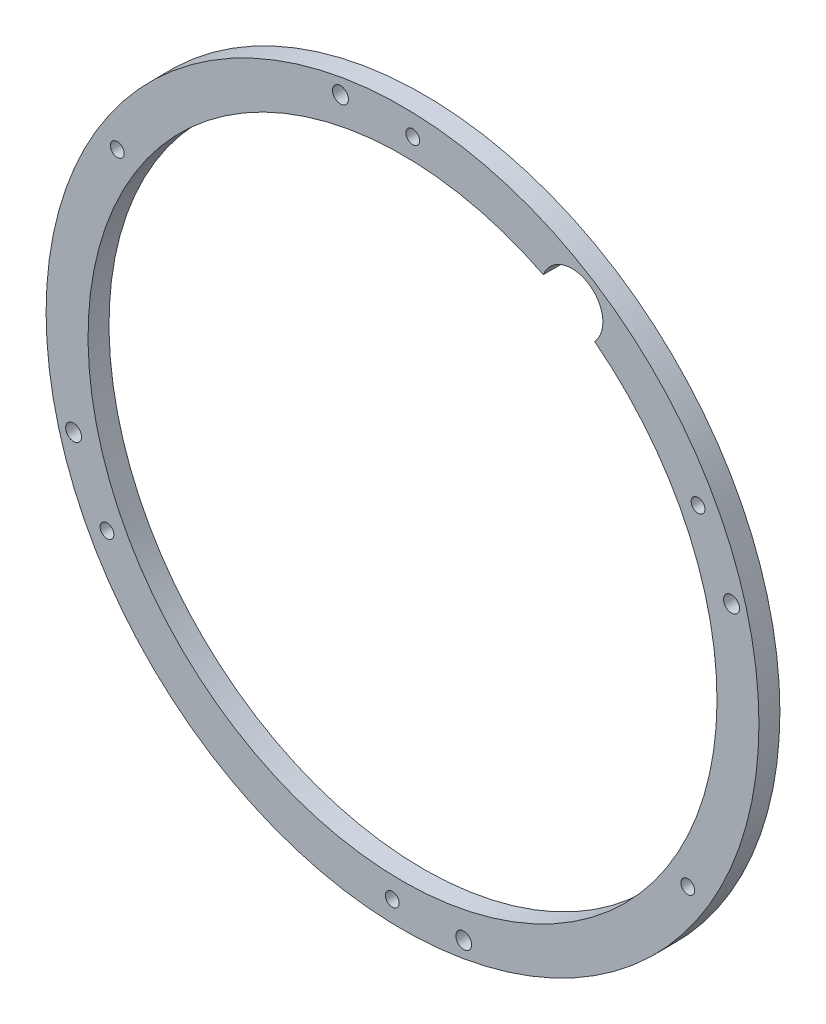
SolidWorks part; units mm, degrees
ref_plane "Front Plane" through (0, 0, 0) normal (0, 0, 1) x (1, 0, 0)
ref_plane "Top Plane" through (0, 0, 0) normal (0, 1, 0) x (1, 0, 0)
ref_plane "Right Plane" through (0, 0, 0) normal (1, 0, 0) x (0, 0, -1)
sketch "Sketch1" plane through (0, 0, 0) normal (0, 0, 1) x (1, 0, 0)
  circle A0 centre (14.5795, 23.25) radius 95.25
  circle A1 centre (14.5795, 23.25) radius 107.95
extrude "Boss-Extrude1" add sketch "Sketch1" along normal blind 6.35
sketch "Sketch2" plane through (0, 0, 0) normal (0, 0, -1) x (-1, 0, 0)
  circle A0 centre (-104.0819, 71.332) radius 2.085 construction
  circle A1 centre (-104.0819, 71.332) radius 2.085
  circle A2 centre (-17.6905, 124.8024) radius 2.085
  circle A3 centre (71.8119, 76.7204) radius 2.085
  circle A4 centre (74.9229, -24.832) radius 2.085
  circle A5 centre (-11.4685, -78.3024) radius 2.085
  circle A6 centre (-100.971, -30.2203) radius 2.085
  circle A8 centre (4.2158, 124.8912) radius 2.413
  circle A10 centre (-114.2203, 50.558) radius 2.413
  point P16 (-14.5795, 23.25)
  dimension "D1" = 6
extrude "Cut-Extrude1" cut sketch "Sketch2" against normal blind 21.336
sketch "Sketch3" plane through (0, 0, 0) normal (0, 0, -1) x (-1, 0, 0)
  circle A0 centre (-65.9242, 105.0103) radius 9.3386
extrude "Cut-Extrude2" cut sketch "Sketch3" against normal through all
sketch "Sketch4" plane through (0, 0, 6.35) normal (0, 0, 1) x (1, 0, 0)
  circle A2 centre (33.1166, -78.2291) radius 2.413
  circle A3 centre (-85.0369, -4.0732) radius 2.413
extrude "Cut-Extrude3" cut sketch "Sketch4" against normal blind 6.35
